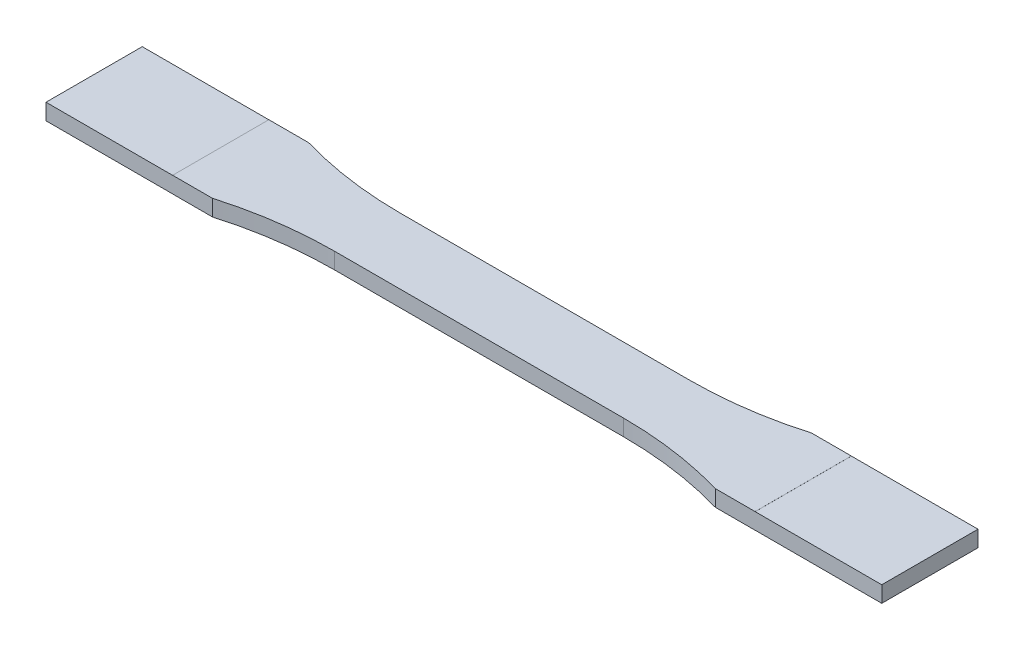
SolidWorks part; units mm, degrees
material "PET"
ref_plane "Alzado" through (0, 0, 0) normal (0, 0, 1) x (1, 0, 0)
ref_plane "Planta" through (0, 0, 0) normal (0, 1, 0) x (1, 0, 0)
ref_plane "Vista lateral" through (0, 0, 0) normal (1, 0, 0) x (0, 0, -1)
sketch "Croquis1" plane through (0, 0, 0) normal (0, 1, 0) x (1, 0, 0)
  line L1 (82.5, -9.5) -> (-82.5, -9.5)
  line L2 (82.5, -9.5) -> (82.5, 9.5)
  line L3 (82.5, 9.5) -> (-82.5, 9.5)
  line L4 (-82.5, -9.5) -> (-82.5, 9.5)
  line L5 (82.5, -9.5) -> (-82.5, 9.5) construction
  line L6 (82.5, 9.5) -> (-82.5, -9.5) construction
  line L7 (28.5, -6.5) -> (-28.5, -6.5)
  line L8 (28.5, -6.5) -> (28.5, 6.5)
  line L9 (28.5, 6.5) -> (-28.5, 6.5)
  line L10 (-28.5, -6.5) -> (-28.5, 6.5)
  line L11 (28.5, -6.5) -> (-28.5, 6.5) construction
  line L12 (28.5, 6.5) -> (-28.5, -6.5) construction
  arc A0 (-49.6424, 9.5) -> (-28.5, 6.5) centre (-28.5, 82.5) ccw
  arc A3 (49.6424, -9.5) -> (28.5, -6.5) centre (28.5, -82.5) ccw
  arc A4 (28.5, 6.5) -> (49.6424, 9.5) centre (28.5, 82.5) ccw
  arc A6 (-28.5, -6.5) -> (-49.6424, -9.5) centre (-28.5, -82.5) ccw
  point P0 (0, 0)
  point P6 (0, 0)
  dimension "D5" = 152
  dimension "D1" = 19
  dimension "D2" = 165
  dimension "D3" = 13
  dimension "D4" = 57
extrude "Saliente-Extruir1" add sketch "Croquis1" along normal mid plane 3.2 contours A6 L10 A0 L3 L4 L1 | A4 L8 A3 L1 L2 L3 | L10 L7 L8 L9
sketch "Croquis2" plane through (0, 1.6, 0) normal (0, 1, 0) x (1, 0, 0)
  line L0 (-57.5, 9.5) -> (-57.5, -9.5)
  line L1 (-49.6424, 9.5) -> (-82.5, 9.5) construction
  line L2 (-49.6424, -9.5) -> (-82.5, -9.5) construction
  line L3 (57.5, 9.5) -> (57.5, -9.5)
  line L4 (82.5, 9.5) -> (49.6424, 9.5) construction
  line L5 (82.5, -9.5) -> (49.6424, -9.5) construction
  line L6 (57.5, 0) -> (-57.5, 0) construction
  line L15 (-28.5, -6.5) -> (28.5, -6.5)
  line L16 (49.6424, -9.5) -> (82.5, -9.5)
  line L17 (82.5, -9.5) -> (82.5, 9.5)
  line L18 (82.5, 9.5) -> (49.6424, 9.5)
  line L19 (28.5, 6.5) -> (-28.5, 6.5)
  line L20 (-49.6424, 9.5) -> (-82.5, 9.5)
  line L21 (-82.5, 9.5) -> (-82.5, -9.5)
  line L22 (-82.5, -9.5) -> (-49.6424, -9.5)
  line L23 (-28.5, -6.5) -> (28.5, -6.5)
  line L24 (49.6424, -9.5) -> (82.5, -9.5)
  line L25 (82.5, -9.5) -> (82.5, 9.5)
  line L26 (82.5, 9.5) -> (49.6424, 9.5)
  line L27 (28.5, 6.5) -> (-28.5, 6.5)
  line L28 (-49.6424, 9.5) -> (-82.5, 9.5)
  line L29 (-82.5, 9.5) -> (-82.5, -9.5)
  line L30 (-82.5, -9.5) -> (-49.6424, -9.5)
  arc A4 (-28.5, -6.5) -> (-49.6424, -9.5) centre (-28.5, -82.5) ccw
  arc A5 (49.6424, -9.5) -> (28.5, -6.5) centre (28.5, -82.5) ccw
  arc A6 (28.5, 6.5) -> (49.6424, 9.5) centre (28.5, 82.5) ccw
  arc A7 (-49.6424, 9.5) -> (-28.5, 6.5) centre (-28.5, 82.5) ccw
  arc A8 (-28.5, -6.5) -> (-49.6424, -9.5) centre (-28.5, -82.5) ccw
  arc A9 (49.6424, -9.5) -> (28.5, -6.5) centre (28.5, -82.5) ccw
  arc A10 (28.5, 6.5) -> (49.6424, 9.5) centre (28.5, 82.5) ccw
  arc A11 (-49.6424, 9.5) -> (-28.5, 6.5) centre (-28.5, 82.5) ccw
  point P14 (0, 0)
  line M5 (49.6424, -9.5) -> (82.5, -9.5)
  line M6 (82.5, -9.5) -> (82.5, 9.5)
  line M7 (82.5, 9.5) -> (49.6424, 9.5)
  line M11 (-49.6424, 9.5) -> (-82.5, 9.5)
  line M12 (-82.5, 9.5) -> (-82.5, -9.5)
  line M13 (-82.5, -9.5) -> (-49.6424, -9.5)
  dimension "D1" = 115
  dimension "D2" = 0
extrude "Cortar-Extruir1" cut sketch "Croquis2" against normal blind 0.01 contours L0 M11 M12 M13 | L3 M7 M5 M6
mirror "Simetría1" about plane through (0, 0, 0) normal (0, 1, 0) of "Cortar-Extruir1"
